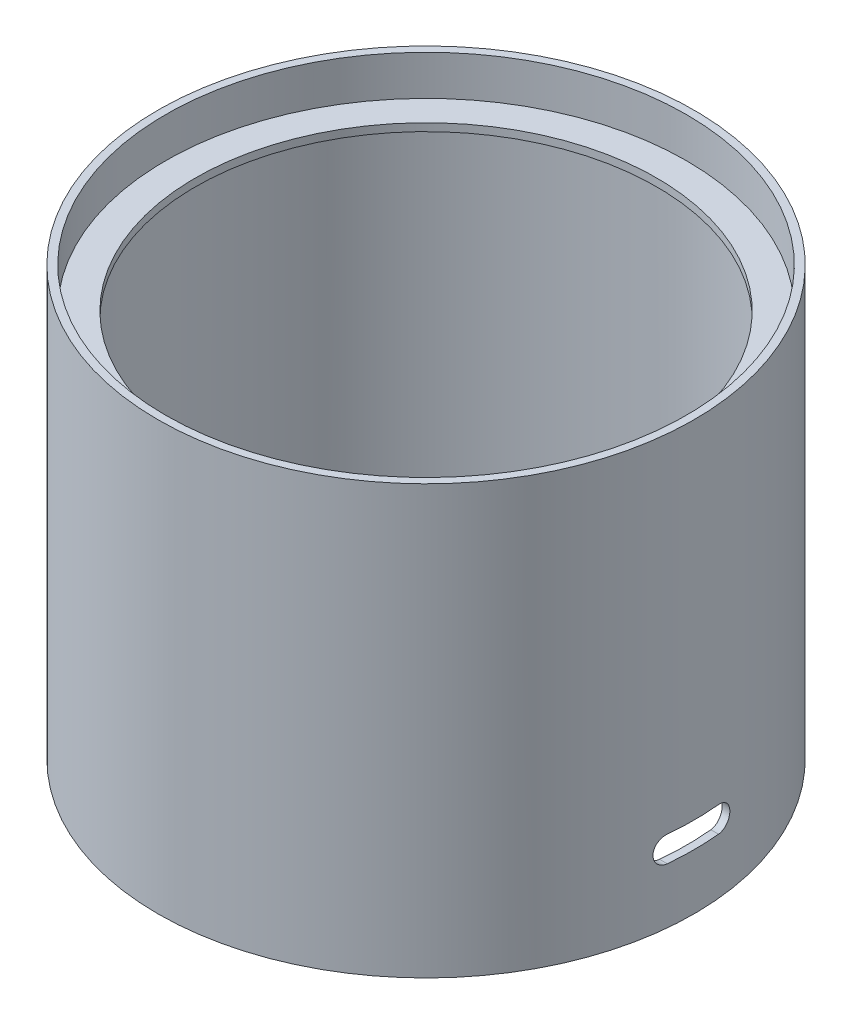
SolidWorks part; units mm, degrees
ref_plane "Front Plane" through (0, 0, 0) normal (0, 0, 1) x (1, 0, 0)
ref_plane "Top Plane" through (0, 0, 0) normal (0, 1, 0) x (1, 0, 0)
ref_plane "Right Plane" through (0, 0, 0) normal (1, 0, 0) x (0, 0, -1)
sketch "Sketch1" plane through (0, 0, 0) normal (0, 1, 0) x (1, 0, 0)
  circle A0 centre (0, 0) radius 101.625
  circle A1 centre (0, 0) radius 104.625
  dimension "D1" = 203.25
  dimension "D2" = 3
extrude "Boss-Extrude1" add sketch "Sketch1" along normal mid plane 167
sketch "Sketch2" plane through (0, 0, 0) normal (0, 0, 1) x (1, 0, 0)
  line L0 (-104.625, -83.5) -> (104.625, -83.5) construction
  line L1 (-20, -33.5) -> (20, -33.5)
  line L2 (-20, -33.5) -> (-20, -83.5)
  line L3 (-20, -83.5) -> (20, -83.5)
  line L4 (20, -33.5) -> (20, -83.5)
  line L5 (-20, -33.5) -> (20, -83.5) construction
  line L6 (-20, -83.5) -> (20, -33.5) construction
  point P0 (0, -58.5)
  point P7 (0, -33.5)
  dimension "D1" = 40
  dimension "D2" = 50
extrude "Cut-Extrude1" cut sketch "Sketch2" against normal up to next
sketch "Sketch3" plane through (0, 0, 0) normal (1, 0, 0) x (0, 0, -1)
  line L0 (-10, -56.809) -> (10, -56.809) construction
  line L1 (-10, -51.809) -> (10, -51.809)
  line L2 (-10, -61.809) -> (10, -61.809)
  arc A0 (-10, -51.809) -> (-10, -61.809) centre (-10, -56.809) ccw
  arc A1 (10, -61.809) -> (10, -51.809) centre (10, -56.809) ccw
  point P2 (0, -56.809)
  dimension "D1" = 10
  dimension "D2" = 20
extrude "Cut-Extrude2" cut sketch "Sketch3" along normal up to next
ref_plane "Plane1" through (0, 67.9, 0) normal (0, 1, 0) x (1, 0, 0)
sketch "Sketch4" plane through (0, 67.9, 0) normal (0, 1, 0) x (1, 0, 0)
  circle A0 centre (0, 0) radius 101.625
  circle A1 centre (0, 0) radius 101.625 construction
  circle A2 centre (0, 0) radius 90
  dimension "D1" = 180
extrude "Boss-Extrude2" add sketch "Sketch4" against normal blind 3
fillet "Fillet1" radius 10 2 edges at (-20, -33.5, -101.1666) (20, -33.5, -101.1666)
